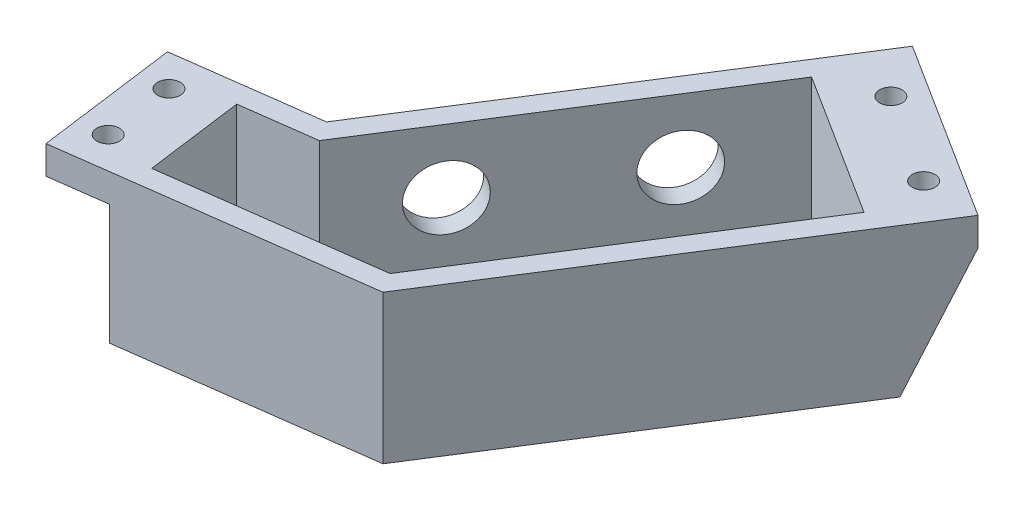
SolidWorks part; units mm, degrees
ref_plane "Спереди" through (0, 0, 0) normal (0, 0, 1) x (1, 0, 0)
ref_plane "Сверху" through (0, 0, 0) normal (0, 1, 0) x (1, 0, 0)
ref_plane "Справа" through (0, 0, 0) normal (1, 0, 0) x (0, 0, -1)
sketch "Sketch1" plane through (0, 0, 0) normal (0, 1, 0) x (1, 0, 0)
  line L0 (0, 0) -> (-19.8234, -2.6518)
  line L1 (-19.8234, -2.6518) -> (-17.1716, -22.4752)
  line L2 (-17.1716, -22.4752) -> (24.8344, -16.856)
  line L3 (24.8344, -16.856) -> (57.4678, 34.6043)
  line L4 (57.4678, 34.6043) -> (32.1325, 50.6705)
  line L5 (32.1325, 50.6705) -> (0, 0)
  line L6 (0, 0) -> (2.6518, -19.8234) construction
  dimension "D1" = 130
  dimension "D2" = 20
  dimension "D3" = 20
  dimension "D4" = 30
  dimension "D5" = 90
  dimension "D6" = 60
extrude "Boss-Extrude1" add sketch "Sketch1" along normal blind 21
sketch "Sketch2" plane through (0, 21, 0) normal (0, 1, 0) x (1, 0, 0)
  line L0 (32.1325, 50.6705) -> (27.8482, 43.9145)
  line L1 (32.1325, 50.6705) -> (0, 0) construction
  line L2 (27.8482, 43.9145) -> (53.1834, 27.8482)
  line L3 (24.8344, -16.856) -> (57.4678, 34.6043) construction
  line L4 (53.1834, 27.8482) -> (57.4678, 34.6043)
  line L5 (57.4678, 34.6043) -> (32.1325, 50.6705)
  line L6 (-19.8234, -2.6518) -> (-17.1716, -22.4752)
  line L7 (-17.1716, -22.4752) -> (-9.2422, -21.4145)
  line L8 (-17.1716, -22.4752) -> (24.8344, -16.856) construction
  line L9 (-9.2422, -21.4145) -> (-11.8941, -1.5911)
  line L10 (0, 0) -> (-19.8234, -2.6518) construction
  line L11 (-11.8941, -1.5911) -> (-19.8234, -2.6518)
  dimension "D1" = 8
extrude "Cut-Extrude1" cut sketch "Sketch2" along normal offset from surface (17 mm away) 4 from surface at -21 up to face at (12.9066, 21, -7.2153) starting at face at (12.9066, 0, -7.2153)
sketch "Sketch3" plane through (0, 21, 0) normal (0, 1, 0) x (1, 0, 0)
  line L0 (28.7751, 39.7743) -> (1.7843, -2.788)
  line L1 (1.7843, -2.788) -> (-8.5228, -4.1668)
  line L2 (-8.5228, -4.1668) -> (-6.6665, -18.0432)
  line L3 (-6.6665, -18.0432) -> (23.0501, -14.068)
  line L4 (23.0501, -14.068) -> (49.0433, 26.9213)
  line L5 (49.0433, 26.9213) -> (28.7751, 39.7743)
  line L6 (28.7751, 39.7743) -> (17.864, 23.073)
  line L7 (32.1325, 50.6705) -> (0, 0) construction
  line L9 (0, 0) -> (-19.8234, -2.6518) construction
  line L10 (-9.2422, -21.4145) -> (-11.8941, -1.5911) construction
  line L11 (-17.1716, -22.4752) -> (24.8344, -16.856) construction
  line L12 (24.8344, -16.856) -> (57.4678, 34.6043) construction
  line L13 (27.8482, 43.9145) -> (53.1834, 27.8482) construction
  dimension "D1" = 3
  dimension "D2" = 3
  dimension "D3" = 3
  dimension "D4" = 3
  dimension "D5" = 3
  dimension "D6" = 3
extrude "Cut-Extrude2" cut sketch "Sketch3" against normal offset from surface (18 mm away) 3 contours L4 L5 L0 L1 L2 L3 up to face at (14.1216, 0, -5.3168)
sketch "Sketch4" plane through (2.5335, 0, 1.6066) normal (0.8445, 0, 0.5355) x (0.5355, 0, -0.8445)
  line L0 (11.6011, 3) -> (11.6011, 21) construction
  line L1 (49, 3) -> (-1.3989, 3) construction
  line L2 (-1.3989, 3) -> (-1.3989, 21) construction
  line L3 (49, 21) -> (-1.3989, 21) construction
  line L4 (1.1011, 4) -> (22.1011, 4) construction
  line L5 (1.1011, 4) -> (1.1011, 20) construction
  line L6 (1.1011, 20) -> (22.1011, 20) construction
  line L7 (22.1011, 4) -> (22.1011, 20) construction
  line L8 (1.1011, 4) -> (22.1011, 20) construction
  line L9 (1.1011, 20) -> (22.1011, 4) construction
  line L10 (11.6011, 12) -> (35.6011, 12) construction
  line L13 (25.1011, 4) -> (46.1011, 4) construction
  line L14 (25.1011, 4) -> (25.1011, 20) construction
  line L15 (25.1011, 20) -> (46.1011, 20) construction
  line L16 (46.1011, 4) -> (46.1011, 20) construction
  line L17 (25.1011, 4) -> (46.1011, 20) construction
  line L18 (25.1011, 20) -> (46.1011, 4) construction
  circle A0 centre (11.6011, 12) radius 4.5
  circle A1 centre (35.6011, 12) radius 4.5
  dimension "D1" = 9
  dimension "D2" = 16
  dimension "D5" = 24
  dimension "D3" = 21
  dimension "D4" = 13
extrude "Cut-Extrude3" cut sketch "Sketch4" against normal through all
sketch "Sketch5" plane through (0, 17, 0) normal (0, -1, 0) x (-1, 0, 0)
  line L0 (-29.9903, 47.2925) -> (-55.3256, 31.2262) construction
  line L1 (-32.1325, 50.6705) -> (-27.8482, 43.9145) construction
  line L2 (-53.1834, 27.8482) -> (-57.4678, 34.6043) construction
  line L3 (15.8587, -2.1215) -> (13.2069, -21.9449) construction
  line L4 (11.8941, -1.5911) -> (19.8234, -2.6518) construction
  line L5 (17.1716, -22.4752) -> (9.2422, -21.4145) construction
  line L8 (-32.1325, 50.6705) -> (-27.8482, 43.9145) construction
  circle A0 centre (-49.414, 34.975) radius 1.6
  circle A1 centre (-36.7464, 43.0082) radius 1.6
  circle A2 centre (13.8699, -16.989) radius 1.6
  circle A3 centre (15.1958, -7.0773) radius 1.6
  point P20 (14.5328, -12.0332)
  dimension "D1" = 3.2
  dimension "D2" = 10
  dimension "D3" = 5
  dimension "D4" = 15
  dimension "D5" = 8
extrude "Cut-Extrude4" cut sketch "Sketch5" against normal through all
sketch "Sketch6" plane through (0, 0, 0) normal (-0.8445, 0, -0.5355) x (-0.5355, 0, 0.8445)
  line L0 (-20, 0) -> (-20, 21) construction
  line L1 (-52, 0) -> (0, 0) construction
  line L2 (-60, 21) -> (0, 21) construction
  line L6 (0, 21) -> (0, 0) construction
  text T0 "<b>      OBS</b>" font "Arial" height 3
  dimension "D1" = 20
extrude "Cut-Extrude5" cut sketch "Sketch6" against normal blind 0.5
sketch "Sketch7" plane through (-8.9205, 0, 1.1933) normal (0.9912, 0, -0.1326) x (-0.1326, 0, -0.9912)
  line L0 (-10, 3) -> (-10, 21) construction
  line L1 (-3, 3) -> (-17, 3) construction
  line L2 (-3, 21) -> (-17, 21) construction
  circle A0 centre (-10, 10) radius 3
  dimension "D1" = 6
  dimension "D2" = 11
extrude "Cut-Extrude6" cut sketch "Sketch7" against normal through all
sketch "Sketch8" plane through (0, 0, 0) normal (-0.8445, 0, -0.5355) x (-0.5355, 0, 0.8445)
  line L0 (-52, 0) -> (-60, 17)
  line L1 (-60, 17) -> (-52, 17)
  line L2 (-52, 17) -> (-52, 0)
extrude "Boss-Extrude2" add sketch "Sketch8" against normal up to surface (30 mm away) up to face at (45.1619, 12.6667, -15.1988)
sketch "Sketch9" plane through (0, 21, 0) normal (0, 1, 0) x (1, 0, 0)
  circle A0 centre (36.7464, 43.0082) radius 1.6
  circle A1 centre (49.414, 34.975) radius 1.6
extrude "Cut-Extrude7" cut sketch "Sketch9" against normal through all
sketch "Sketch10" plane through (0, 21, 0) normal (0, 1, 0) x (1, 0, 0)
  circle A0 centre (36.7464, 43.0082) radius 3.5
  circle A1 centre (49.414, 34.975) radius 3.5
  dimension "D1" = 7
extrude "Cut-Extrude8" cut sketch "Sketch10" against normal through all from offset 4 offset against normal yes
sketch "Sketch11" plane through (0, 0, 0) normal (-0.1326, 0, -0.9912) x (-0.9912, 0, 0.1326)
  line L0 (7, 0) -> (7, 21) construction
  line L1 (0, 0) -> (12, 0) construction
  line L2 (0, 21) -> (20, 21) construction
  line L3 (12, 17) -> (12, 0) construction
  text T0 "<b>  1/ADF/2</b>" font "Arial" height 3
  dimension "D1" = 5
extrude "Cut-Extrude9" cut sketch "Sketch11" against normal blind 0.5
sketch "Sketch13" plane through (0, 0, 0) normal (-0.8445, 0, -0.5355) x (-0.5355, 0, 0.8445)
  line L0 (-44, 0) -> (-44, 21) construction
  line L1 (-52, 0) -> (0, 0) construction
  line L2 (-60, 21) -> (0, 21) construction
  text T0 "<b>     DIR G</b>" font "Arial" height 3
  dimension "D1" = 8
extrude "Cut-Extrude11" cut sketch "Sketch13" against normal blind 0.5
